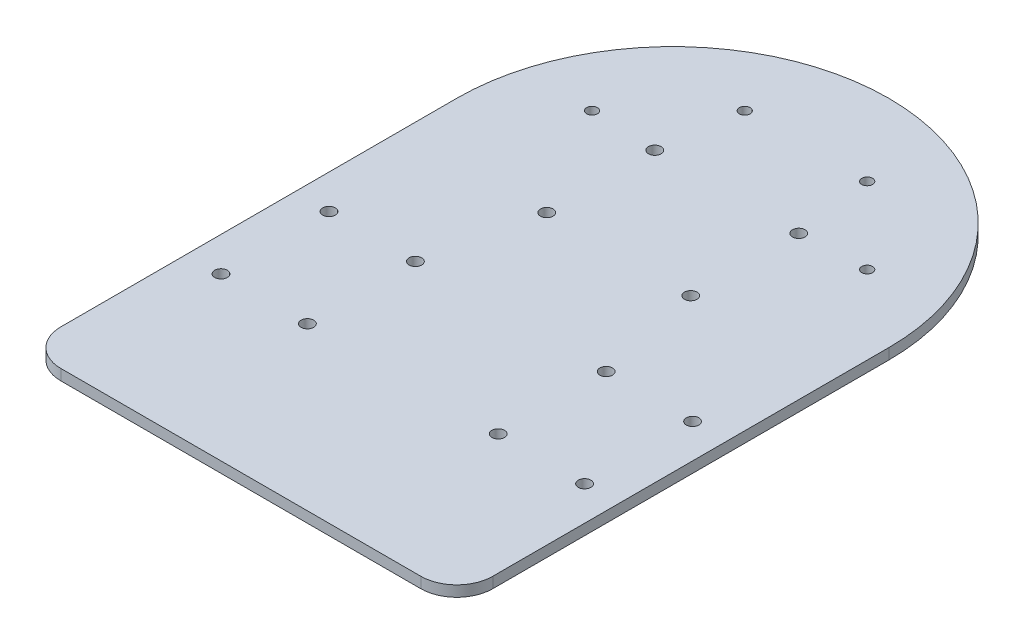
SolidWorks part; units mm, degrees
material "3003 Alloy"
ref_plane "Front Plane" through (0, 0, 0) normal (0, 0, 1) x (1, 0, 0)
ref_plane "Top Plane" through (0, 0, 0) normal (0, 1, 0) x (1, 0, 0)
ref_plane "Right Plane" through (0, 0, 0) normal (1, 0, 0) x (0, 0, -1)
sketch "Sketch1" plane through (0, 0, 0) normal (0, 1, 0) x (1, 0, 0)
  line L2 (-60, 60) -> (-60, -60)
  line L3 (-60, -60) -> (60, -60)
  line L4 (60, 60) -> (60, -60)
  arc A0 (60, 60) -> (-60, 60) centre (0, 60) ccw
extrude "Boss-Extrude3" add sketch "Sketch1" along normal blind 3
fillet "Fillet3" radius 10 2 edges at (60, 1.5, 60) (-60, 1.5, 60)
sketch "Sketch4" plane through (0, 3, 0) normal (0, 1, 0) x (1, 0, 0)
  circle A0 centre (-26.5, -15) radius 1.75
  circle A1 centre (-50.5, -15) radius 1.75
  circle A2 centre (-50.5, 15) radius 1.75
  circle A3 centre (-26.5, 15) radius 1.75
  dimension "D1" = 2
  dimension "D2" = 2
extrude "Cut-Extrude1" cut sketch "Sketch4" against normal up to next (3 mm away)
mirror "Mirror1" about plane through (0, 0, 0) normal (1, 0, 0) of "Cut-Extrude1"
sketch "Sketch5" plane through (0, 3, 0) normal (0, 1, 0) x (1, 0, 0)
  circle A0 centre (20, 75) radius 1.75
  circle A1 centre (-20, 75) radius 1.75
  circle A2 centre (-20, 45) radius 1.75
  circle A3 centre (20, 45) radius 1.75
  dimension "D1" = 2
  dimension "D2" = 2
extrude "Cut-Extrude2" cut sketch "Sketch5" against normal up to next
sketch "Sketch6" plane through (0, 3, 0) normal (0, 1, 0) x (1, 0, 0)
  line L0 (0, -1.65) -> (0, 1.65) construction
  circle A0 centre (-38.2132, 75.7868) radius 1.5
  circle A1 centre (-17, 97) radius 1.5
  circle A2 centre (17, 97) radius 1.5
  circle A3 centre (38.2132, 75.7868) radius 1.5
  point P8 (-96.2153, 3)
  point P9 (-96.2153, 117.2198)
extrude "Cut-Extrude3" cut sketch "Sketch6" against normal up to next
